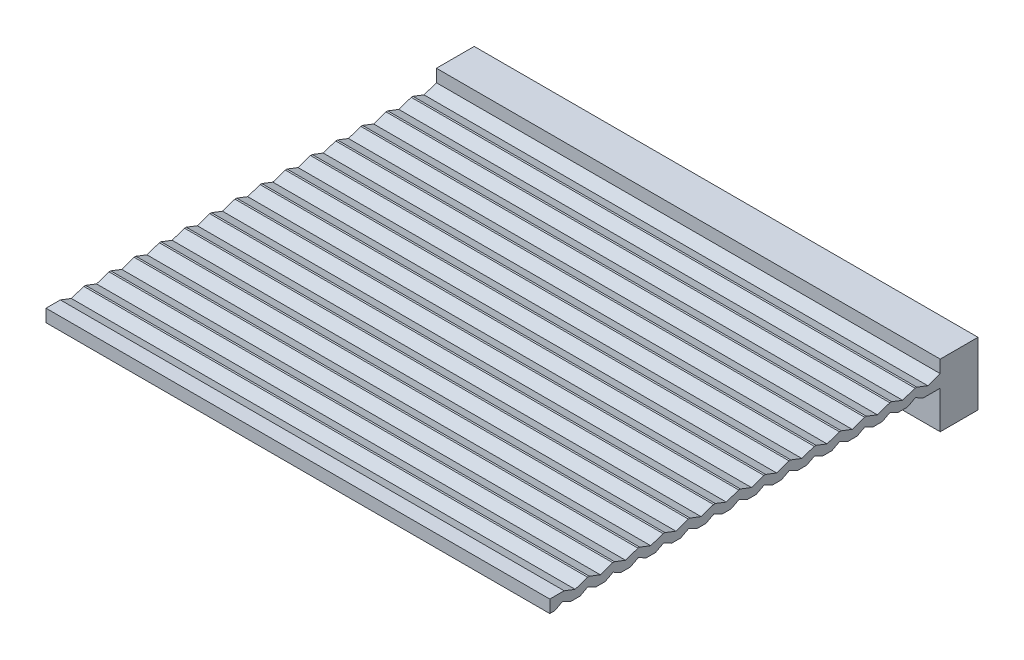
SolidWorks part; units mm, degrees
ref_plane "Front Plane" through (0, 0, 0) normal (0, 0, 1) x (1, 0, 0)
ref_plane "Top Plane" through (0, 0, 0) normal (0, 1, 0) x (1, 0, 0)
ref_plane "Right Plane" through (0, 0, 0) normal (1, 0, 0) x (0, 0, -1)
sketch "Sketch1" plane through (0, 0, 0) normal (0, 1, 0) x (1, 0, 0)
  line L1 (0, 0) -> (400, 0)
  line L2 (0, 0) -> (0, 30)
  line L3 (0, 30) -> (400, 30)
  line L4 (400, 0) -> (400, 30)
  dimension "D1" = 30
  dimension "D2" = 400
extrude "Boss-Extrude1" add sketch "Sketch1" along normal blind 50
sketch "Sketch2" plane through (0, 0, 0) normal (0, 0, 1) x (1, 0, 0)
  line L0 (0, 50) -> (400, 50) construction
  line L1 (0, 40) -> (400, 40)
  line L2 (0, 40) -> (0, 30)
  line L3 (0, 30) -> (400, 30)
  line L4 (400, 40) -> (400, 30)
  line L5 (0, 50) -> (0, 0) construction
  line L6 (400, 50) -> (400, 0) construction
  dimension "D1" = 10
  dimension "D2" = 10
extrude "Boss-Extrude2" add sketch "Sketch2" along normal blind 310
sketch "Sketch3" plane through (0, 0, 0) normal (-1, 0, 0) x (0, 0, 1)
  line L0 (0, 40) -> (9.8674, 36.6243)
  line L1 (9.8674, 36.6243) -> (18.6179, 40)
  line L2 (310, 40) -> (0, 40) construction
  line L3 (18.6179, 40) -> (0, 40)
  line L4 (13.2834, 30) -> (19.7384, 33.3028)
  line L5 (310, 30) -> (0, 30) construction
  line L6 (19.7384, 33.3028) -> (26.0128, 30)
  line L7 (26.0128, 30) -> (13.2834, 30)
extrude "Cut-Extrude1" cut sketch "Sketch3" against normal up to next (400 mm away)
pattern_linear "LPattern1" count 15 spacing 20 along (0, 0, 1) of "Cut-Extrude1"
